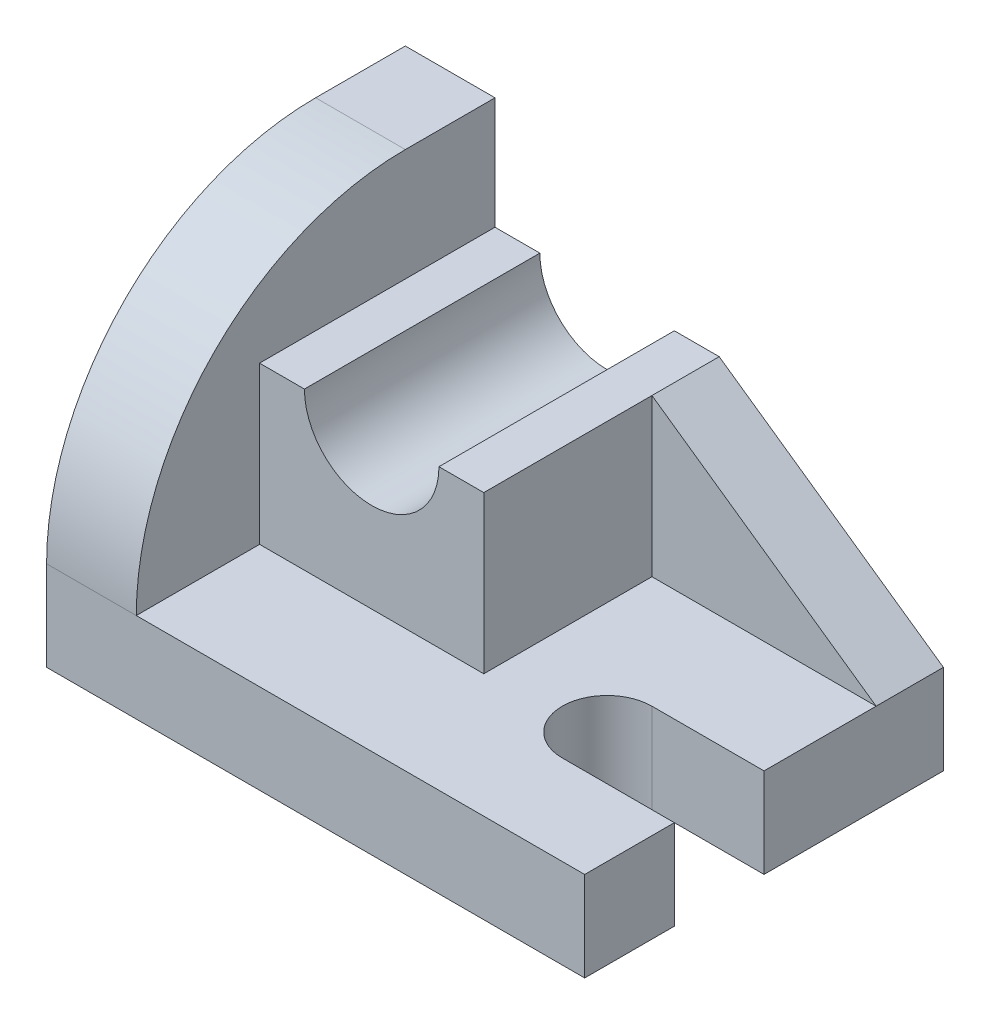
SolidWorks part; units mm, degrees
ref_plane "Front Plane" through (0, 0, 0) normal (0, 0, 1) x (1, 0, 0)
ref_plane "Top Plane" through (0, 0, 0) normal (0, 1, 0) x (1, 0, 0)
ref_plane "Right Plane" through (0, 0, 0) normal (1, 0, 0) x (0, 0, -1)
sketch "Sketch1" plane through (0, 0, 0) normal (0, 1, 0) x (1, 0, 0)
  line L1 (0, 0) -> (96, 0)
  line L2 (0, 0) -> (0, 64)
  line L3 (0, 64) -> (96, 64)
  line L4 (96, 0) -> (96, 64)
  dimension "D1" = 96
  dimension "D2" = 64
extrude "Boss-Extrude1" add sketch "Sketch1" along normal blind 16
sketch "Sketch2" plane through (0, 16, 0) normal (0, 1, 0) x (1, 0, 0)
  line L0 (96, 24) -> (76, 24) construction
  line L1 (96, 0) -> (96, 64) construction
  line L2 (96, 16) -> (76, 16)
  line L3 (96, 32) -> (76, 32)
  line L4 (0, 0) -> (96, 0) construction
  arc A0 (96, 16) -> (96, 32) centre (96, 24) ccw
  arc A1 (76, 32) -> (76, 16) centre (76, 24) ccw
  point P4 (86, 24)
  dimension "D2" = 8
  dimension "D1" = 20
  dimension "D3" = 16
extrude "Cut-Extrude1" cut sketch "Sketch2" against normal blind 16
sketch "Sketch3" plane through (0, 0, 0) normal (-1, 0, 0) x (0, 0, 1)
  line L1 (-64, 0) -> (0, 0)
  line L2 (-64, 0) -> (-64, 64)
  line L3 (-64, 64) -> (-48, 64)
  line L4 (0, 0) -> (0, 16)
  arc A0 (-48, 64) -> (0, 16) centre (-48, 16) cw
  point P7 (0, 64)
  dimension "D3" = 48
  dimension "D1" = 64
  dimension "D2" = 64
extrude "Boss-Extrude2" add sketch "Sketch3" against normal blind 16
sketch "Sketch4" plane through (0, 16, 0) normal (0, 1, 0) x (1, 0, 0)
  line L0 (16, 0) -> (96, 0) construction
  line L1 (16, 64) -> (56, 64)
  line L2 (16, 64) -> (16, 22)
  line L3 (16, 22) -> (56, 22)
  line L4 (56, 64) -> (56, 22)
  dimension "D1" = 40
  dimension "D2" = 22
extrude "Boss-Extrude3" add sketch "Sketch4" along normal blind 28
sketch "Sketch5" plane through (0, 0, -22) normal (0, 0, 1) x (1, 0, 0)
  line L0 (16, 44) -> (56, 44) construction
  circle A0 centre (36, 44) radius 12
  dimension "D1" = 24
extrude "Cut-Extrude2" cut sketch "Sketch5" against normal up to next
sketch "Sketch7" plane through (0, 0, -64) normal (0, 0, -1) x (-1, 0, 0)
  line L0 (-56, 44) -> (-96, 16)
  line L10 (-16, 44) -> (-24, 44)
  line L11 (-48, 44) -> (-56, 44)
  line L12 (-56, 44) -> (-56, 16)
  line L13 (-56, 16) -> (-96, 16)
  line L14 (-96, 16) -> (-96, 0)
  line L15 (-96, 0) -> (0, 0)
  line L16 (0, 0) -> (0, 64)
  line L17 (0, 64) -> (-16, 64)
  line L18 (-16, 64) -> (-16, 44)
  line L21 (-56, 44) -> (-56, 16)
  line L22 (-56, 16) -> (-96, 16)
  arc A1 (-48, 44) -> (-24, 44) centre (-36, 44) ccw
  dimension "D1" = 0
extrude "Boss-Extrude4" add sketch "Sketch7" against normal blind 12
